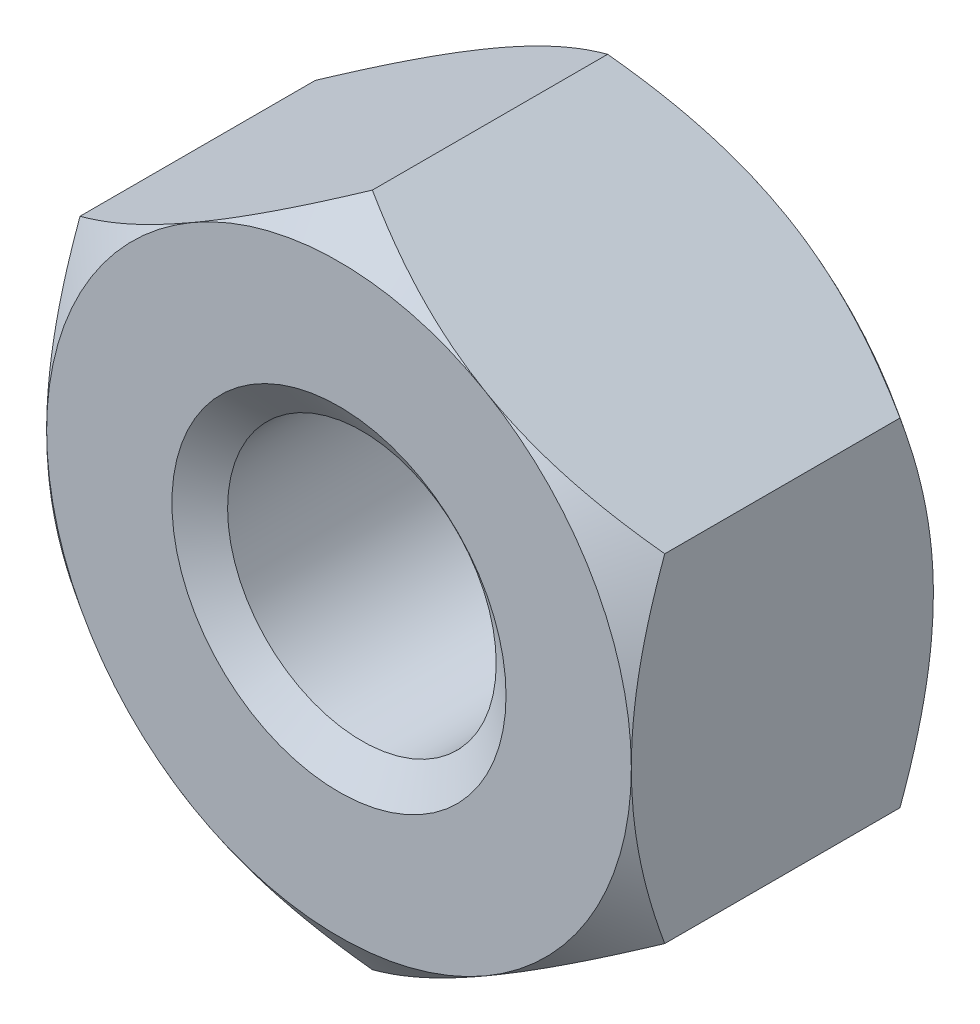
SolidWorks part; units mm, degrees
extrude "BaseNut" add sketch "BaseNutSke" against normal blind 5.7404
sketch "BaseNutSke" plane through (0, 0, 0) normal (0, 0, 1) x (1, 0, 0)
  line L6 (5.5563, 3.2079) -> (5.5563, -3.2079)
  line L7 (-5.5562, 3.2079) -> (-5.5562, -3.2079)
  line L8 (5.5563, 3.2079) -> (0, 6.4158)
  line L9 (0, 6.4158) -> (-5.5562, 3.2079)
  line L10 (-5.5562, -3.2079) -> (0, -6.4158)
  line L11 (0, -6.4158) -> (5.5563, -3.2079)
  circle A0 centre (0, 0) radius 2.5527
  dimension "Tap_drill" = 5.1054
  dimension "Width_flats" = 11.1125
  dimension "D2" = 5.5562
  dimension "D3" = 5.5562
  dimension "D1" = 120
  dimension "D4" = 5.5562
cosmetic thread "ThreadCosmetic" [suppressed] parameters "Thread_major"=6.35
pattern_linear "ThdSchPat" [suppressed]
revolve "ThreadSchematic" [suppressed] cut sketch "ThdSchSke" angle 360 about L6
sketch "ThdSchSke" plane through (0, 0, 0) normal (0, 1, 0) x (1, 0, 0)
  line L0 (-3.175, 0.0254) -> (-2.5527, 0.4611)
  line L1 (-2.5527, 0.4611) -> (-1.2763, 0.4611)
  line L2 (-1.2763, 0.4611) -> (-1.2763, -0.4103)
  line L3 (-1.2763, -0.4103) -> (-2.5527, -0.4103)
  line L4 (-2.5527, -0.4103) -> (-3.175, 0.0254)
  line L5 (-3.175, 1.27) -> (3.175, 1.27) construction
  line L6 (0, 1.27) -> (0, -2.9874) construction
  line L7 (0, 5.2793) -> (0, 0.4357) construction
  dimension "Thread_major" = 6.35
  dimension "SideAngle" = 55
  dimension "Advance" = 1.27
  dimension "D1" = 0.0254
ref_plane "Plane1" through (0, 0, 0) normal (0, 0, 1) x (1, 0, 0)
ref_plane "Plane2" through (0, 0, 0) normal (0, 1, 0) x (1, 0, 0)
ref_plane "Plane3" through (0, 0, 0) normal (1, 0, 0) x (0, 0, -1)
sketch "Sketch4" plane through (0, 0, 0) normal (1, 0, 0) x (0, 0, -1)
  line L0 (5.7404, 5.5562) -> (5.334, 5.5562)
  line L1 (5.7404, 5.5562) -> (5.7404, 19.1158)
  line L2 (5.334, 19.1158) -> (5.7404, 19.1158)
  line L3 (5.334, 19.1158) -> (5.334, 5.5562)
  line L4 (0, 0) -> (34.925, 0) construction
  line L6 (5.7404, 3.2079) -> (5.7404, 6.4158) construction
  line L7 (0, 5.5562) -> (-12.7, 5.5562)
  line L8 (0, 3.2079) -> (0, 6.4158) construction
  line L9 (0.635, 6.4158) -> (0.635, 19.1158)
  line L10 (0.635, 19.1158) -> (-12.7, 19.1158)
  line L11 (-12.7, 19.1158) -> (-12.7, 5.5562)
  line L12 (0, 5.5562) -> (0.635, 6.4158)
  line L14 (0, 3.2079) -> (0, -3.2079) construction
  line L15 (5.7404, 6.4158) -> (0, 6.4158) construction
  dimension "D1" = 5.5562
  dimension "D2" = 0.635
  dimension "D3" = 12.7
  dimension "D4" = 12.7
revolve "Bearing-Face" [suppressed] cut sketch "Sketch4" angle 360 about L4
sketch "Sketch3" plane through (0, 0, 0) normal (1, 0, 0) x (0, 0, -1)
  line L0 (5.7404, 5.5562) -> (5.1054, 6.4158)
  line L1 (5.1054, 6.4158) -> (5.1054, 19.1158)
  line L2 (5.1054, 19.1158) -> (18.4404, 19.1158)
  line L3 (18.4404, 19.1158) -> (18.4404, 5.5563)
  line L4 (18.4404, 5.5563) -> (5.7404, 5.5562)
  line L5 (5.7404, 3.2079) -> (5.7404, 6.4158) construction
  line L6 (5.7404, 6.4158) -> (0, 6.4158) construction
  line L7 (0, 0) -> (38.6776, 0) construction
  line L8 (5.7404, 0) -> (0, 0) construction
  line L9 (2.8702, 6.4158) -> (2.8702, 44.222) construction
  line L10 (0.635, 19.1158) -> (-12.7, 19.1158)
  line L11 (-12.7, 19.1158) -> (-12.7, 5.5563)
  line L12 (-12.7, 5.5563) -> (0, 5.5562)
  line L13 (0, 5.5562) -> (0.635, 6.4158)
  line L14 (0.635, 6.4158) -> (0.635, 19.1158)
  line L16 (5.7404, 6.4158) -> (0, 6.4158) construction
  dimension "D1" = 5.5562
  dimension "D2" = 0.635
  dimension "D4" = 12.7
  dimension "D3" = 12.7
revolve "Double-Chamfer" cut sketch "Sketch3" angle 360 about L7
sketch "Sketch5" plane through (0, 0, 0) normal (1, 0, 0) x (0, 0, -1)
  line L0 (5.715, 3.175) -> (5.2357, 2.4905)
  line L1 (5.7658, 3.175) -> (5.715, 3.175)
  line L2 (5.7658, 3.175) -> (5.7658, 2.4905)
  line L3 (5.7658, 2.4905) -> (5.2357, 2.4905)
  line L6 (-0.0508, 3.175) -> (0, 3.175)
  line L7 (0, 3.175) -> (0.4793, 2.4905)
  line L9 (0.4793, 2.4905) -> (-0.0508, 2.4905)
  line L10 (-0.0508, 2.4905) -> (-0.0508, 3.175)
  line L11 (25.0375, 0) -> (38.388, 0) construction
  line L12 (5.7404, 0) -> (0, 0) construction
  dimension "D1" = 35
  dimension "D2" = 0.0508
  dimension "ThreadMajor" = 3.175
  dimension "Offset1" = 5.7658
revolve "EndChamfer" cut sketch "Sketch5" angle 360 about L11
equation "\"D2@BaseNutSke\" = \"Width_flats@BaseNutSke\" / 2"
equation "\"D3@BaseNutSke\" = \"Width_flats@BaseNutSke\" / 2"
equation "\"D1@Sketch3\" = \"Width_flats@BaseNutSke\" /2"
equation "\"D2@Sketch3\" = \"Thread_major@ThreadCosmetic\" *.1"
equation "\"D1@Sketch4\" = \"D2@BaseNutSke\""
equation "\"D2@Sketch4\" = \"Thread_major@ThreadCosmetic\" *.10"
equation "\"D4@BaseNutSke\" = \"D3@BaseNutSke\""
equation "\"Thread_major@ThdSchSke\" = \"Thread_major@ThreadCosmetic\""
equation "\"Tap_Drill@ThdSchSke\" = \"Tap_drill@BaseNutSke\""
equation "\"OverCut@ThdSchSke\" = \"Tap_Drill@ThdSchSke\" * 0.5"
equation "\"Num_threads@ThdSchPat\" = int(  ( \"Thickness@BaseNut\" - 0.002 ) / \"Advance@ThdSchSke\" + 0.999 )  + 1"
equation "\"Advance@ThdSchPat\" = ( \"Thickness@BaseNut\" - 0.002 ) /  (\"Num_threads@ThdSchPat\" - 1) 'relax it"
equation "' \"Num_threads@ThdSchPat\" = \"Num_threads@ThdSchPat\" - sgn( \"Num_threads@ThdSchPat\" - 1) '---chamfered tips only---"
equation "\"ThreadMajor@Sketch5\" = \"Thread_major@ThreadCosmetic\" * 0.5"
equation "\"ChamferDepth@Sketch5\" = (\"Thread_major@ThreadCosmetic\" - \"Tap_drill@BaseNutSke\") * 0.55"
equation "\"Offset1@Sketch5\" = \"Thickness@BaseNut\" + 0.001"
equation "\"Offset2@Sketch5\" = \"Offset1@Sketch5\" + 0.002"
